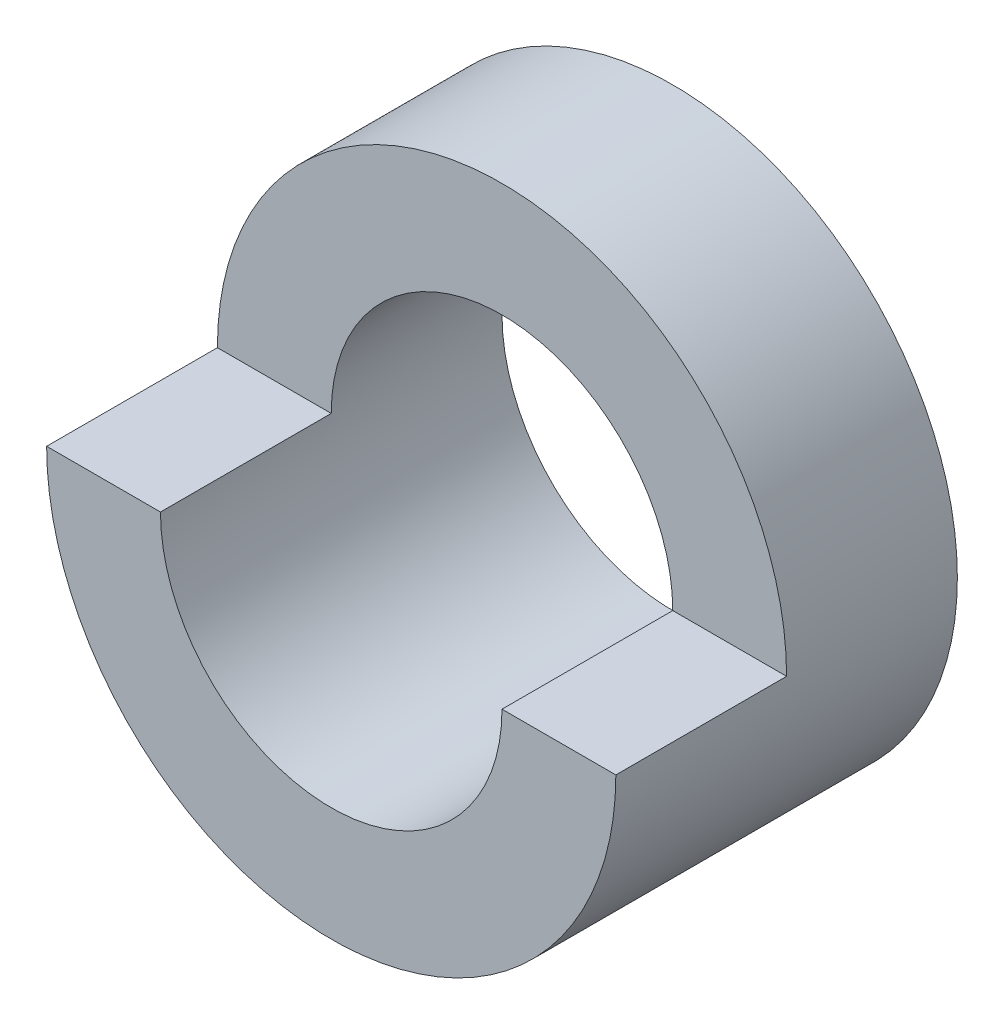
SolidWorks part; units mm, degrees
ref_plane "Front Plane" through (0, 0, 0) normal (0, 0, 1) x (1, 0, 0)
ref_plane "Top Plane" through (0, 0, 0) normal (0, 1, 0) x (1, 0, 0)
ref_plane "Right Plane" through (0, 0, 0) normal (1, 0, 0) x (0, 0, -1)
sketch "Sketch1" plane through (0, 0, 0) normal (0, 0, 1) x (1, 0, 0)
  circle A0 centre (0, 0) radius 50
  dimension "D1" = 100
extrude "Boss-Extrude1" add sketch "Sketch1" along normal blind 60
sketch "Sketch2" plane through (0, 0, 60) normal (0, 0, 1) x (1, 0, 0)
  circle A0 centre (0, 0) radius 30
  dimension "D1" = 60
extrude "Cut-Extrude1" cut sketch "Sketch2" against normal blind 60
sketch "Sketch3" plane through (0, 0, 60) normal (0, 0, 1) x (1, 0, 0)
  line L0 (-50, 0) -> (-30, 0)
  line L1 (30, 0) -> (50, 0)
  arc A0 (30, 0) -> (-30, 0) centre (0, 0) ccw
  circle A1 centre (0, 0) radius 30 construction
  arc A2 (50, 0) -> (-50, 0) centre (0, 0) ccw
  circle A3 centre (0, 0) radius 50 construction
  dimension "D1" = 20
  dimension "D2" = 20
extrude "Cut-Extrude2" cut sketch "Sketch3" against normal blind 30
